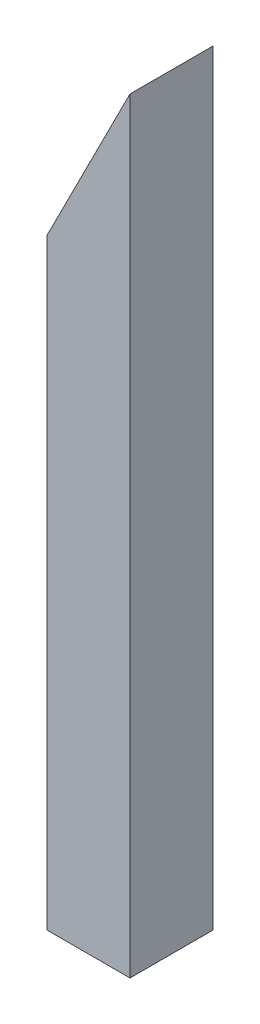
SolidWorks part; units mm, degrees
material "AISI 302"
ref_plane "Front Plane" through (0, 0, 0) normal (0, 0, 1) x (1, 0, 0)
ref_plane "Top Plane" through (0, 0, 0) normal (0, 1, 0) x (1, 0, 0)
ref_plane "Right Plane" through (0, 0, 0) normal (1, 0, 0) x (0, 0, -1)
sketch "Sketch1" plane through (0, 0, 0) normal (0, 0, 1) x (1, 0, 0)
  line L0 (0, 0) -> (203.2, 0)
  line L1 (203.2, 0) -> (203.2, 1873.504)
  line L2 (203.2, 1873.504) -> (0, 1472.1071)
  line L3 (0, 1472.1071) -> (0, 0)
  dimension "D1" = 203.2
  dimension "D2" = 1873.504
  dimension "D3" = 26.85
extrude "Boss-Extrude1" add sketch "Sketch1" along normal blind 203.2
sketch "Sketch2" plane through (0, 0, 0) normal (0, -1, 0) x (1, 0, 0)
  line L12 (184.15, 184.15) -> (19.05, 184.15)
  line L13 (184.15, 19.05) -> (184.15, 184.15)
  line L14 (19.05, 19.05) -> (184.15, 19.05)
  line L15 (19.05, 184.15) -> (19.05, 19.05)
  line L16 (184.15, 184.15) -> (19.05, 184.15)
  line L17 (184.15, 19.05) -> (184.15, 184.15)
  line L18 (19.05, 19.05) -> (184.15, 19.05)
  line L19 (19.05, 184.15) -> (19.05, 19.05)
  dimension "D1" = 19.05
extrude "Cut-Extrude1" cut sketch "Sketch2" against normal through all both and the other way through all
